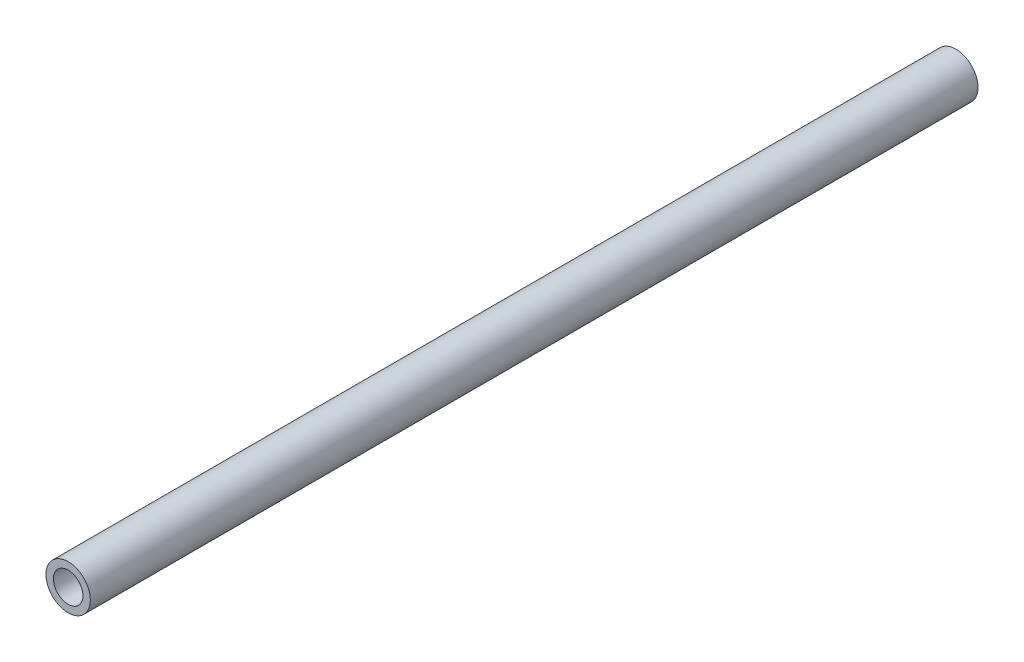
SolidWorks part; units mm, degrees
ref_plane "Front Plane" through (0, 0, 0) normal (0, 0, 1) x (1, 0, 0)
ref_plane "Top Plane" through (0, 0, 0) normal (0, 1, 0) x (1, 0, 0)
ref_plane "Right Plane" through (0, 0, 0) normal (1, 0, 0) x (0, 0, -1)
sketch "Sketch2" plane through (0, 0, 0) normal (0, 0, 1) x (1, 0, 0)
  circle A0 centre (0, 0) radius 3
  circle A1 centre (0, 0) radius 2
  dimension "D1" = 6
extrude "Boss-Extrude1" add sketch "Sketch2" along normal blind 120
